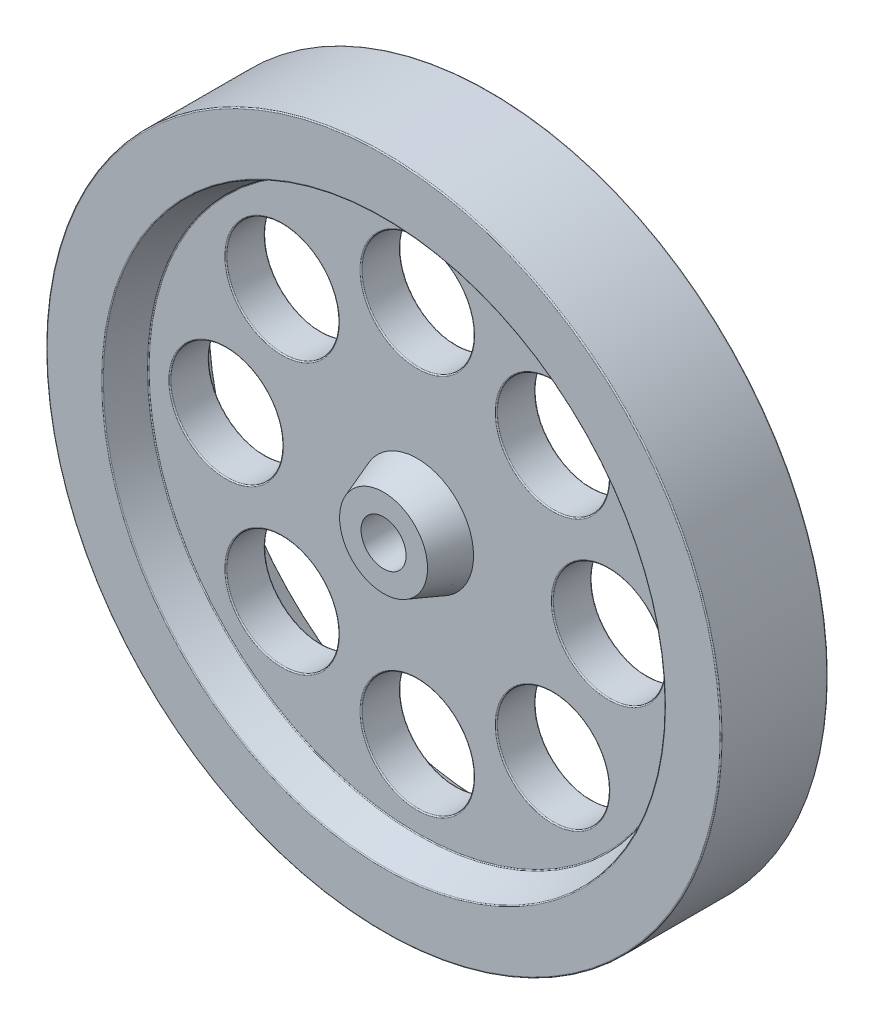
SolidWorks part; units mm, degrees
material "Stainless Steel (ferritic)"
ref_plane "Front Plane" through (0, 0, 0) normal (0, 0, 1) x (1, 0, 0)
ref_plane "Top Plane" through (0, 0, 0) normal (0, 1, 0) x (1, 0, 0)
ref_plane "Right Plane" through (0, 0, 0) normal (1, 0, 0) x (0, 0, -1)
sketch "Sketch1" plane through (0, 0, 0) normal (0, 0, 1) x (1, 0, 0)
  circle A0 centre (0, 0) radius 30
  circle A1 centre (0, 0) radius 25
  point P23 (0, 0)
  dimension "D1" = 60
  dimension "D2" = 50
sketch "Sketch3" plane through (0, 0, 0) normal (0, 0, 1) x (1, 0, 0)
  circle A0 centre (0, 0) radius 30
  dimension "D1" = 60
extrude "Boss-Extrude2" add sketch "Sketch3" along normal mid plane 9.5
sketch "Sketch4" plane through (0, 0, 4.75) normal (0, 0, 1) x (1, 0, 0)
  circle A0 centre (0, 0) radius 25
  dimension "D1" = 50
extrude "Cut-Extrude1" cut sketch "Sketch4" against normal blind 3 draft 20
mirror "Mirror1" about plane through (0, 0, 0) normal (0, 0, 1) of "Cut-Extrude1"
sketch "Sketch5" plane through (0, 0, 1.75) normal (0, 0, 1) x (1, 0, 0)
  circle A0 centre (0, 0) radius 17 construction
  circle A1 centre (0, 17) radius 5
  circle A2 centre (12.0208, 12.0208) radius 5
  circle A3 centre (17, 0) radius 5
  circle A4 centre (12.0208, -12.0208) radius 5
  circle A5 centre (0, -17) radius 5
  circle A6 centre (-12.0208, -12.0208) radius 5
  circle A7 centre (-17, 0) radius 5
  circle A8 centre (-12.0208, 12.0208) radius 5
  point P21 (0, 0)
  dimension "D1" = 34
  dimension "D2" = 10
  dimension "D3" = 8
extrude "Cut-Extrude2" cut sketch "Sketch5" against normal up to next
fillet "Fillet1" radius 0.1 22 edges at (22, 0, 1.75) (12, 0, -1.75) (17.0208, -12.0208, 1.75) (7.0208, -12.0208, -1.75) (5, -17, 1.75) (-5, -17, -1.75) (-7.0208, -12.0208, 1.75) (-17.0208, -12.0208, -1.75) (-12, 0, 1.75) (-22, 0, -1.75) (-7.0208, 12.0208, 1.75) (-17.0208, 12.0208, -1.75) (5, 17, 1.75) (-5, 17, -1.75) (17.0208, 12.0208, 1.75) (7.0208, 12.0208, -1.75) (-23.9081, 0, -1.75) (25, 0, -4.75) (30, 0, -4.75) (23.9081, 0, 1.75) (25, 0, 4.75) (30, 0, 4.75)
sketch "Sketch8" plane through (0, 0, 1.75) normal (0, 0, 1) x (1, 0, 0)
  circle A0 centre (0, 0) radius 5
  dimension "D1" = 10
extrude "Boss-Extrude4" add sketch "Sketch8" along normal blind 3 draft 20
sketch "Sketch9" plane through (0, 0, -1.75) normal (0, 0, -1) x (-1, 0, 0)
  circle A0 centre (0, 0) radius 5
  dimension "D1" = 10
extrude "Boss-Extrude5" add sketch "Sketch9" along normal blind 3 draft 20
sketch "Sketch10" plane through (0, 0, 0) normal (1, 0, 0) x (0, 0, -1)
  line L0 (-4.75, 2) -> (1.25, 2)
  line L1 (-4.75, 29.9) -> (-4.75, -29.9) construction
  line L2 (1.25, 2) -> (1.25, 1.5)
  line L3 (1.25, 1.5) -> (3.75, 1.5)
  line L4 (3.75, 1.5) -> (4.75, 2.5)
  line L5 (4.75, -29.9) -> (4.75, 29.9) construction
  line L6 (4.75, 2.5) -> (4.75, 0)
  line L7 (4.75, 0) -> (-4.75, 0)
  line L8 (-4.75, 0) -> (-4.75, 2)
  dimension "D1" = 45
  dimension "D2" = 6
  dimension "D3" = 2
  dimension "D4" = 2.5
  dimension "D5" = 1.5
revolve "Cut-Revolve1" cut sketch "Sketch10" angle 360 about L7
